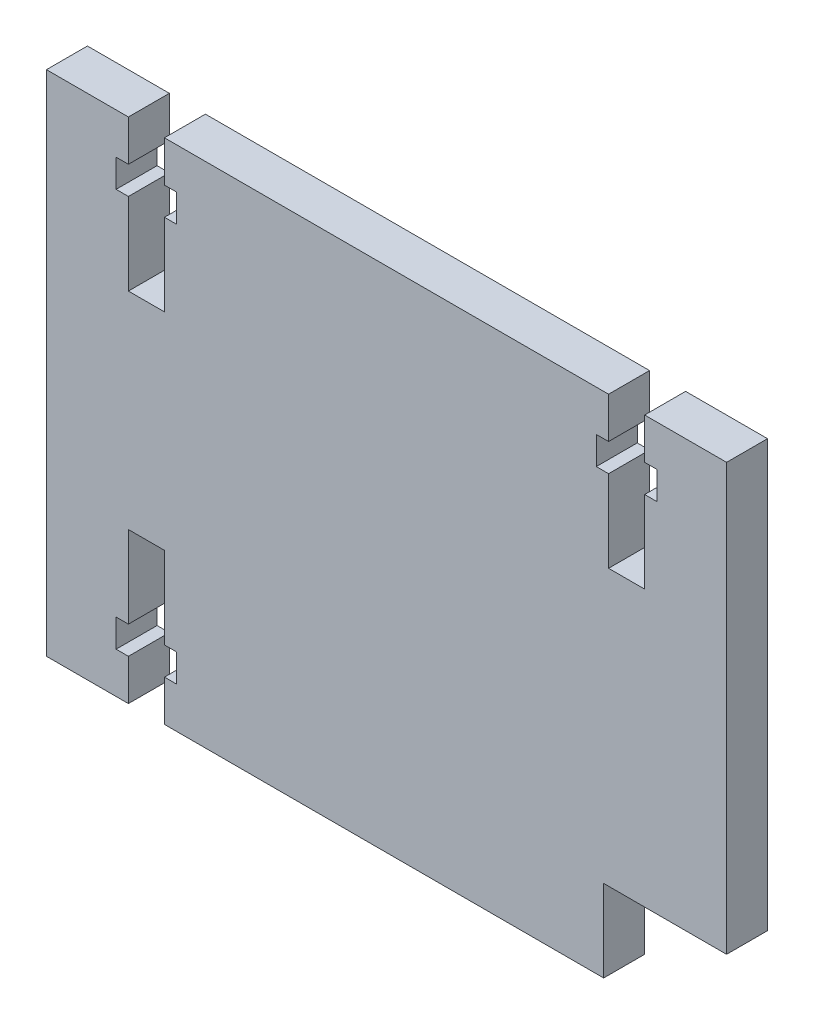
SolidWorks part; units mm, degrees
ref_plane "Front Plane" through (0, 0, 0) normal (0, 0, 1) x (1, 0, 0)
ref_plane "Top Plane" through (0, 0, 0) normal (0, 1, 0) x (1, 0, 0)
ref_plane "Right Plane" through (0, 0, 0) normal (1, 0, 0) x (0, 0, -1)
sketch "Sketch1" plane through (0, 0, 0) normal (0, 0, 1) x (1, 0, 0)
  line L1 (-41.5, 31) -> (41.5, 31)
  line L2 (-41.5, 31) -> (-41.5, -31)
  line L3 (-41.5, -31) -> (41.5, -31)
  line L4 (41.5, 31) -> (41.5, -31)
  dimension "D1" = 83
  dimension "D2" = 41.5
  dimension "D3" = 62
  dimension "D4" = 31
extrude "Boss-Extrude1" add sketch "Sketch1" along normal blind 5
sketch "Sketch2" plane through (0, 0, 5) normal (0, 0, 1) x (1, 0, 0)
  line L0 (0, 0) -> (-32.0835, 0) construction
  line L1 (41.5, -31) -> (26.5, -31)
  line L2 (41.5, -31) -> (41.5, -21)
  line L3 (41.5, -21) -> (26.5, -21)
  line L4 (26.5, -31) -> (26.5, -21)
  line L5 (0, 0) -> (0, 20.1899) construction
  dimension "D1" = 10
  dimension "D2" = 15
extrude "Cut-Extrude1" cut sketch "Sketch2" against normal blind 10
sketch "Sketch3" plane through (0, 0, 5) normal (0, 0, 1) x (1, 0, 0)
  line L0 (-29.3, 10.8) -> (-29.3, 25.6452) construction
  line L1 (-27.1, 22.6) -> (-27.1, 12.6)
  line L2 (-31.5, 26) -> (-31.5, 31)
  line L3 (-25.6, 26) -> (-27.1, 26)
  line L4 (-25.6, 22.6) -> (-25.6, 26)
  line L5 (-27.1, 22.6) -> (-25.6, 22.6)
  line L6 (-33, 26) -> (-31.5, 26)
  line L7 (-33, 22.6) -> (-33, 26)
  line L8 (-31.5, 22.6) -> (-33, 22.6)
  line L9 (-31.5, 12.6) -> (-27.1, 12.6)
  line L10 (-27.1, 31) -> (-27.1, 26)
  line L11 (-31.5, 31) -> (-27.1, 31)
  line L12 (-31.5, 12.6) -> (-31.5, 22.6)
  line L13 (41.5, 31) -> (-41.5, 31) construction
  line L14 (-41.5, 31) -> (-41.5, -31) construction
  line L15 (0, 0) -> (0, 26) construction
  line L16 (0, 0) -> (-34.9357, 0) construction
  line L17 (29.3, 10.8) -> (29.3, 25.6452) construction
  line L18 (31.5, 12.6) -> (31.5, 22.6)
  line L19 (31.5, 31) -> (27.1, 31)
  line L20 (27.1, 31) -> (27.1, 26)
  line L21 (31.5, 12.6) -> (27.1, 12.6)
  line L22 (31.5, 22.6) -> (33, 22.6)
  line L23 (33, 22.6) -> (33, 26)
  line L24 (33, 26) -> (31.5, 26)
  line L25 (27.1, 22.6) -> (25.6, 22.6)
  line L26 (25.6, 22.6) -> (25.6, 26)
  line L27 (25.6, 26) -> (27.1, 26)
  line L28 (31.5, 26) -> (31.5, 31)
  line L29 (27.1, 22.6) -> (27.1, 12.6)
  line L30 (-29.3, -10.8) -> (-29.3, -25.6452) construction
  line L31 (-31.5, -12.6) -> (-31.5, -22.6)
  line L32 (-31.5, -31) -> (-27.1, -31)
  line L33 (-27.1, -31) -> (-27.1, -26)
  line L34 (-31.5, -12.6) -> (-27.1, -12.6)
  line L35 (-31.5, -22.6) -> (-33, -22.6)
  line L36 (-33, -22.6) -> (-33, -26)
  line L37 (-33, -26) -> (-31.5, -26)
  line L38 (-27.1, -22.6) -> (-25.6, -22.6)
  line L39 (-25.6, -22.6) -> (-25.6, -26)
  line L40 (-25.6, -26) -> (-27.1, -26)
  line L41 (-31.5, -26) -> (-31.5, -31)
  line L42 (-27.1, -22.6) -> (-27.1, -12.6)
  dimension "D1" = 5
  dimension "D2" = 3.4
  dimension "D3" = 10
  dimension "D4" = 2.2
  dimension "D5" = 4.4
  dimension "D6" = 1.5
  dimension "D7" = 1.5
  dimension "D8" = 10
extrude "Cut-Extrude2" cut sketch "Sketch3" against normal blind 5
